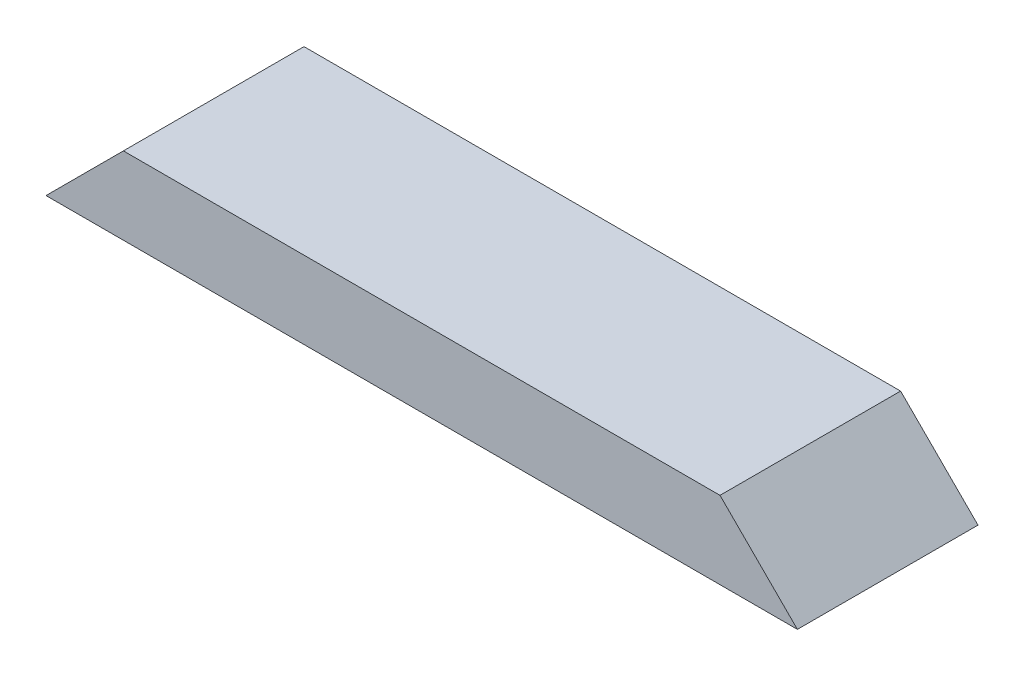
SolidWorks part; units mm, degrees
ref_plane "Front Plane" through (0, 0, 0) normal (0, 0, 1) x (1, 0, 0)
ref_plane "Top Plane" through (0, 0, 0) normal (0, 1, 0) x (1, 0, 0)
ref_plane "Right Plane" through (0, 0, 0) normal (1, 0, 0) x (0, 0, -1)
sketch "Sketch1" plane through (0, 0, 0) normal (0, 1, 0) x (1, 0, 0)
  line L1 (0, 0) -> (369.8875, 0)
  line L2 (0, 0) -> (0, 88.9)
  line L3 (0, 88.9) -> (369.8875, 88.9)
  line L4 (369.8875, 0) -> (369.8875, 88.9)
  dimension "D1" = 88.9
  dimension "D2" = 369.8875
extrude "Boss-Extrude1" add sketch "Sketch1" along normal blind 38.1
sketch "Sketch2" plane through (0, 0, 0) normal (0, 0, 1) x (1, 0, 0)
  line L0 (0, 0) -> (38.1, 38.1)
  line L1 (0, 38.1) -> (369.8875, 38.1) construction
  line L2 (0, 38.1) -> (0, 0)
  line L3 (369.8875, 0) -> (331.7875, 38.1)
  line L4 (331.7875, 38.1) -> (369.8875, 38.1)
  line L5 (369.8875, 38.1) -> (369.8875, 0)
  line L6 (38.1, 38.1) -> (0, 38.1)
  dimension "D1" = 38.1
  dimension "D2" = 38.1
extrude "Cut-Extrude1" cut sketch "Sketch2" against normal through all
